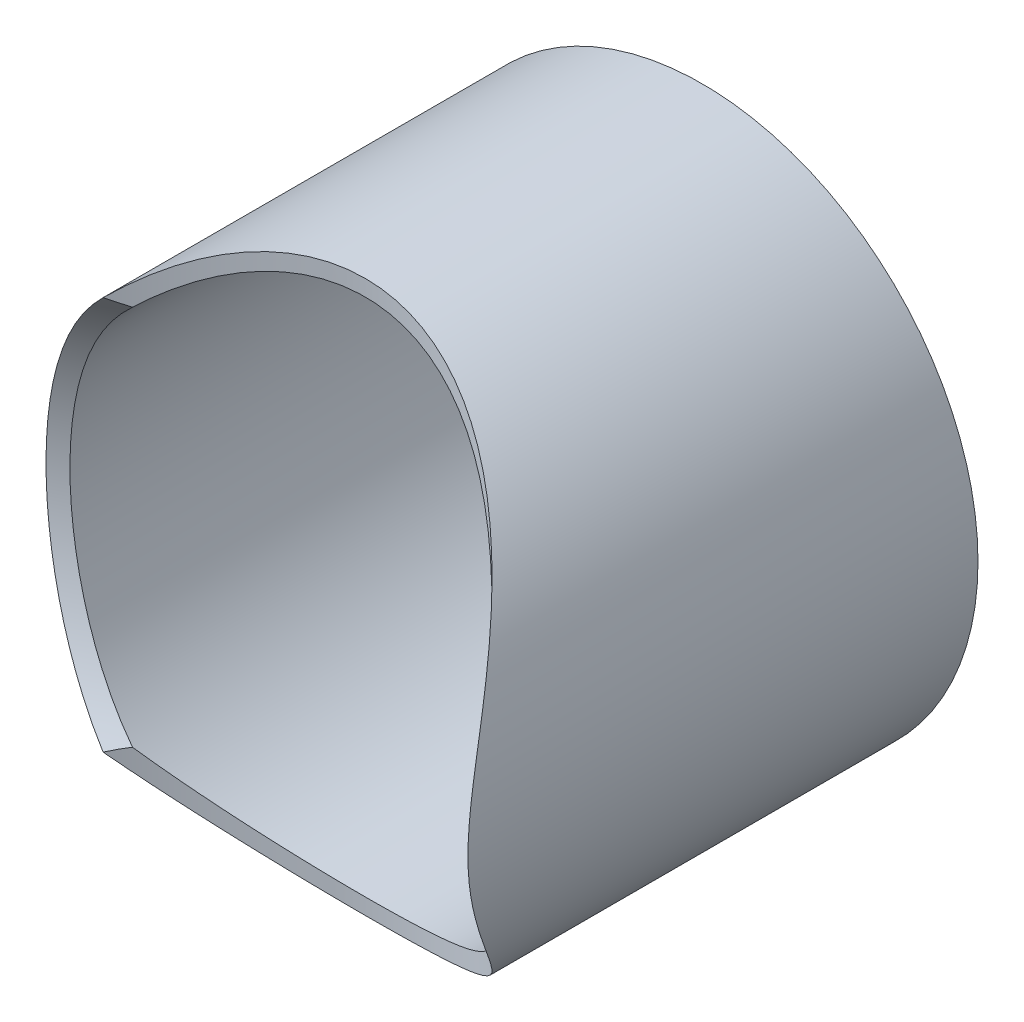
SolidWorks part; units mm, degrees
ref_plane "Front Plane" through (0, 0, 0) normal (0, 0, 1) x (1, 0, 0)
ref_plane "Top Plane" through (0, 0, 0) normal (0, 1, 0) x (1, 0, 0)
ref_plane "Right Plane" through (0, 0, 0) normal (1, 0, 0) x (0, 0, -1)
sketch "Sketch1" plane through (0, 0, 0) normal (0, 0, 1) x (1, 0, 0)
  circle A0 centre (316.7831, 0) radius 15.85 construction
  circle A1 centre (316.7831, 0) radius 15.85 construction
  circle A2 centre (316.7831, 0) radius 17.15
  circle A3 centre (316.7831, 0) radius 16.15
  dimension "D1" = 1.3
  dimension "D2" = 0.3
extrude "Boss-Extrude1" add sketch "Sketch1" against normal blind 40
sketch "Sketch2" plane through (-60.876, 0, 29.6912) normal (0.8988, 0, -0.4384) x (-0.4384, 0, -0.8988)
  circle A0 centre (-138.8686, 0) radius 22.225 construction
  circle A1 centre (-138.8686, 0) radius 22.225
extrude "Cut-Extrude1" cut sketch "Sketch2" along normal up to vertex (352.4535 mm away)
sketch "Sketch3" plane through (0, -34.5, 0) normal (0, -1, 0) x (1, 0, 0)
  circle A0 centre (316.7831, 0) radius 19.05 construction
  circle A1 centre (316.7831, 0) radius 19.05
extrude "Cut-Extrude2" cut sketch "Sketch3" against normal through all
